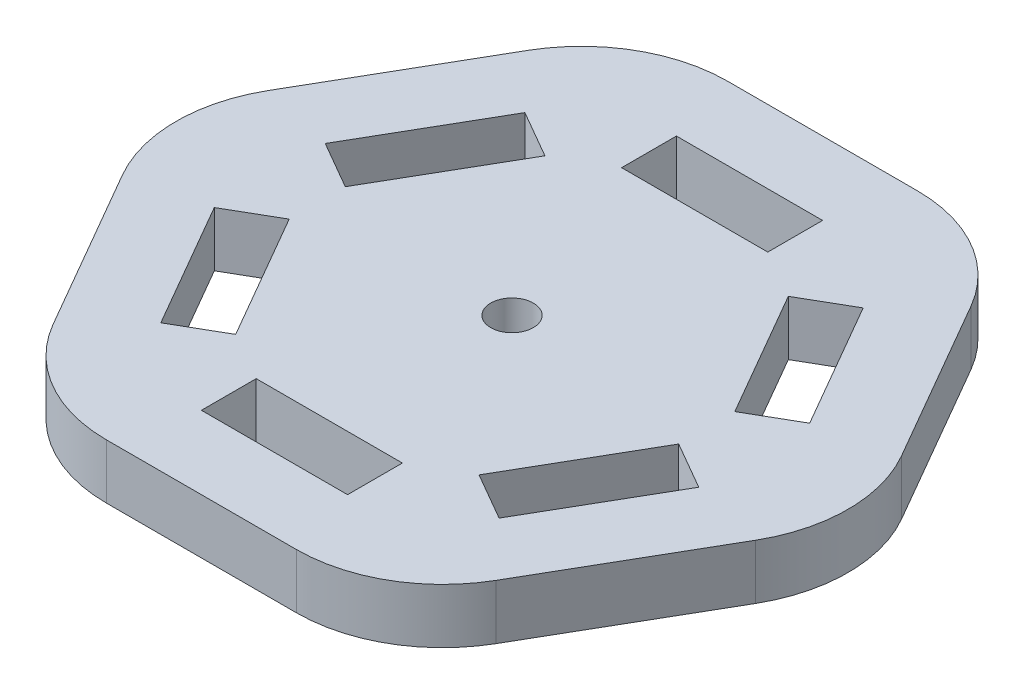
SolidWorks part; units mm, degrees
ref_plane "前视基准面" through (0, 0, 0) normal (0, 0, 1) x (1, 0, 0)
ref_plane "上视基准面" through (0, 0, 0) normal (0, 1, 0) x (1, 0, 0)
ref_plane "右视基准面" through (0, 0, 0) normal (1, 0, 0) x (0, 0, -1)
sketch "草图1" plane through (0, 0, 0) normal (0, 1, 0) x (1, 0, 0)
  line L0 (0, 0) -> (0, 19.5) construction
  line L1 (13.8875, 14.9462) -> (9.9904, 12.6962)
  line L2 (6, 15) -> (-6, 15)
  line L3 (19.8875, 4.5538) -> (13.8875, 14.9462)
  line L4 (19.8875, 4.5538) -> (15.9904, 2.3038)
  line L5 (15.9904, 2.3038) -> (9.9904, 12.6962)
  line L6 (19.8875, -4.5538) -> (15.9904, -2.3038)
  line L7 (13.8875, -14.9462) -> (19.8875, -4.5538)
  line L8 (6, 19.5) -> (-6, 19.5)
  line L9 (13.8875, -14.9462) -> (9.9904, -12.6962)
  line L10 (9.9904, -12.6962) -> (15.9904, -2.3038)
  line L11 (6, -19.5) -> (6, -15)
  line L12 (-6, -19.5) -> (6, -19.5)
  line L13 (29.4449, 0) -> (14.7224, 25.5)
  line L14 (14.7224, 25.5) -> (-14.7224, 25.5)
  line L15 (-14.7224, 25.5) -> (-29.4449, 0)
  line L16 (-29.4449, 0) -> (-14.7224, -25.5)
  line L17 (-14.7224, -25.5) -> (14.7224, -25.5)
  line L18 (14.7224, -25.5) -> (29.4449, 0)
  line L19 (6, 19.5) -> (6, 15)
  line L20 (-6, 19.5) -> (-6, 15)
  line L21 (-6, -19.5) -> (-6, -15)
  line L22 (-6, -15) -> (6, -15)
  line L23 (-13.8875, -14.9462) -> (-9.9904, -12.6962)
  line L24 (-19.8875, -4.5538) -> (-13.8875, -14.9462)
  line L25 (-19.8875, -4.5538) -> (-15.9904, -2.3038)
  line L26 (-15.9904, -2.3038) -> (-9.9904, -12.6962)
  line L27 (-19.8875, 4.5538) -> (-15.9904, 2.3038)
  line L28 (-13.8875, 14.9462) -> (-19.8875, 4.5538)
  line L29 (-13.8875, 14.9462) -> (-9.9904, 12.6962)
  line L30 (-9.9904, 12.6962) -> (-15.9904, 2.3038)
  circle A2 centre (0, 0) radius 1.75
  arc A3 (-22.0836, -12.75) -> (-22.0836, 12.75) centre (0, 0) ccw construction
  point P44 (0, 0)
  dimension "D3" = 3.5
  dimension "D1" = 15
  dimension "D2" = 4.5
  dimension "D4" = 6
  dimension "D5" = 12
  dimension "D6" = 6
extrude "凸台-拉伸1" add sketch "草图1" along normal blind 4.5
fillet "圆角1" radius 12 6 edges at (-14.7224, 2.25, 25.5) (-29.4449, 2.25, 0) (-14.7224, 2.25, -25.5) (14.7224, 2.25, -25.5) (29.4449, 2.25, 0) (14.7224, 2.25, 25.5)
